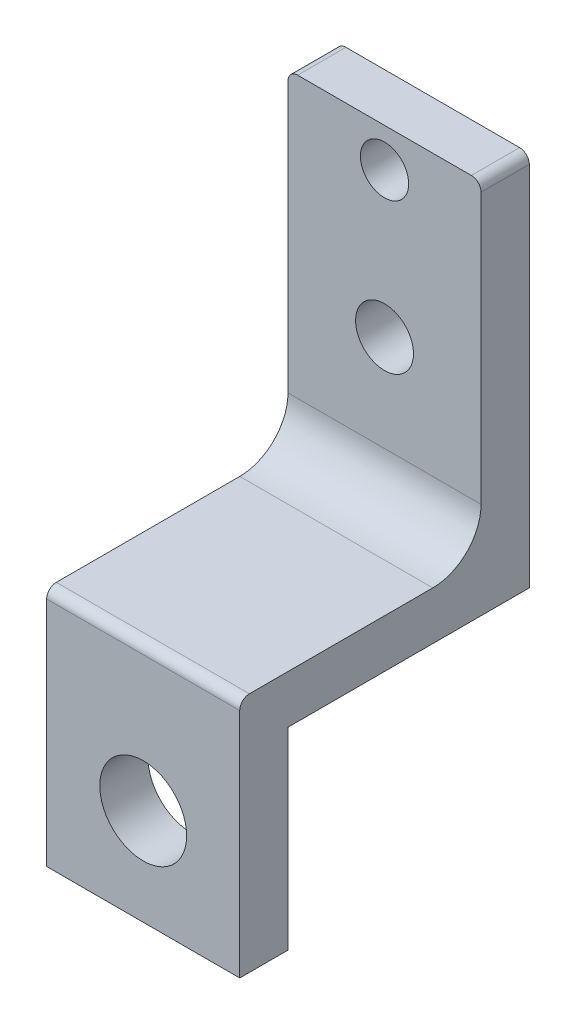
SolidWorks part; units mm, degrees
material "6061 Alloy"
ref_plane "前视基准面" through (0, 0, 0) normal (0, 0, 1) x (1, 0, 0)
ref_plane "上视基准面" through (0, 0, 0) normal (0, 1, 0) x (1, 0, 0)
ref_plane "右视基准面" through (0, 0, 0) normal (1, 0, 0) x (0, 0, -1)
other "Configuration Table"
sketch "Sketch1" plane through (0, 0, 0) normal (0, 0, 1) x (1, 0, 0)
  line L0 (0, 0) -> (0, 30) construction
  line L2 (-10, 10) -> (-10, -10)
  line L3 (-10, -10) -> (10, -10)
  line L4 (10, 10) -> (10, -10)
  line L5 (-10, 10) -> (10, -10) construction
  line L6 (-10, -10) -> (10, 10) construction
  line L7 (0, 30) -> (0, 45) construction
  line L8 (0, 45) -> (0, 49) construction
  line L9 (10, 49) -> (-10, 49)
  line L10 (-10, 49) -> (-10, 10)
  line L11 (10, 49) -> (10, 10)
  circle A0 centre (0, 0) radius 4.5
  circle A1 centre (0, 30) radius 3 construction
  circle A2 centre (0, 45) radius 2.5 construction
  dimension "D1" = 20
  dimension "D3" = 9
  dimension "D5" = 6
  dimension "D7" = 5
  dimension "D2" = 20
  dimension "D4" = 30
  dimension "D6" = 15
  dimension "D8" = 4
extrude "Boss-Extrude1" add sketch "Sketch1" along normal blind 5
sketch "Sketch2" plane through (0, 0, 0) normal (0, 0, -1) x (-1, 0, 0)
  line L1 (-10, -10) -> (10, -10) construction
  line L2 (-10, -10) -> (-10, 10) construction
  line L3 (-10, 10) -> (10, 10) construction
  line L4 (10, -10) -> (10, 10) construction
  line L5 (-10, -10) -> (10, 10) construction
  line L6 (-10, 10) -> (10, -10) construction
  line L7 (-10, 49) -> (10, 49)
  line L8 (-10, 49) -> (-10, 10)
  line L9 (-10, 10) -> (10, 10)
  line L10 (10, 49) -> (10, 10)
  point P0 (0, 0)
  dimension "D1" = 20
  dimension "D2" = 20
extrude "Boss-Extrude2" add sketch "Sketch2" along normal blind 25
sketch "Sketch3" plane through (10, 0, 0) normal (1, 0, 0) x (0, 0, -1)
  line L0 (0, 10) -> (0, 15) construction
  line L1 (0, 15) -> (-5, 15)
  line L2 (-5, -10) -> (-5, 49) construction
  line L3 (-5, 15) -> (-5, 49)
  line L4 (-5, 49) -> (20, 49)
  line L5 (-5, 49) -> (25, 49) construction
  line L6 (20, 49) -> (20, 15)
  line L7 (20, 15) -> (0, 15)
  dimension "D1" = 5
extrude "Cut-Extrude1" cut sketch "Sketch3" against normal blind 30
sketch "Sketch4" plane through (0, 0, -20) normal (0, 0, 1) x (1, 0, 0)
  circle A0 centre (0, 45) radius 2.5
  circle A1 centre (0, 30) radius 3
extrude "Cut-Extrude2" cut sketch "Sketch4" against normal blind 30
fillet "Fillet1" radius 5 1 edges at (0, 15, -20)
fillet "Fillet2" radius 1 3 edges at (0, 15, 5) (-10, 49, -22.5) (10, 49, -22.5)
mirror "Mirror1" [suppressed]
delete or keep bodies "Body-Delete/Keep 1" [suppressed] type delete bodies bodies 109
